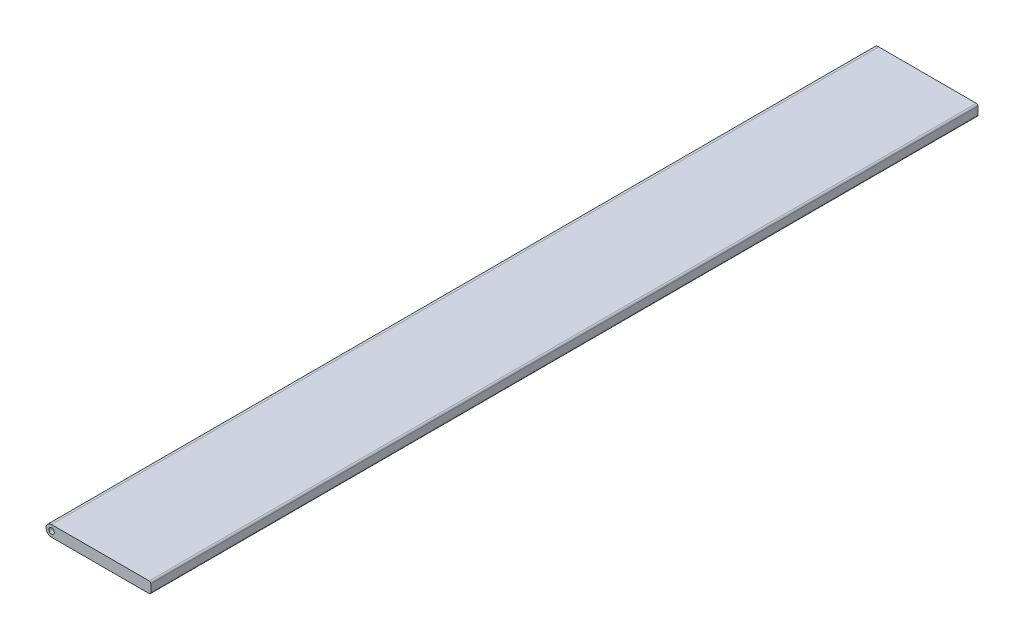
SolidWorks part; units mm, degrees
ref_plane "Front" through (0, 0, 0) normal (0, 0, 1) x (1, 0, 0)
ref_plane "Top" through (0, 0, 0) normal (0, 1, 0) x (1, 0, 0)
ref_plane "Right" through (0, 0, 0) normal (1, 0, 0) x (0, 0, -1)
sketch "草图1" plane through (0, 0, 0) normal (0, 0, 1) x (1, 0, 0)
  line L0 (0, -1) -> (18, -1)
  line L1 (0, 1) -> (18, 1)
  line L2 (18, 1) -> (18, -1)
  circle A0 centre (0, 0) radius 1
  circle A3 centre (0, 0) radius 0.5
  dimension "D1" = 2
  dimension "D4" = 1
  dimension "D2" = 18
extrude "凸台-拉伸1" add sketch "草图1" along normal blind 150
fillet "圆角1" radius 0.3 2 edges at (18, -1, 75) (18, 1, 75)
